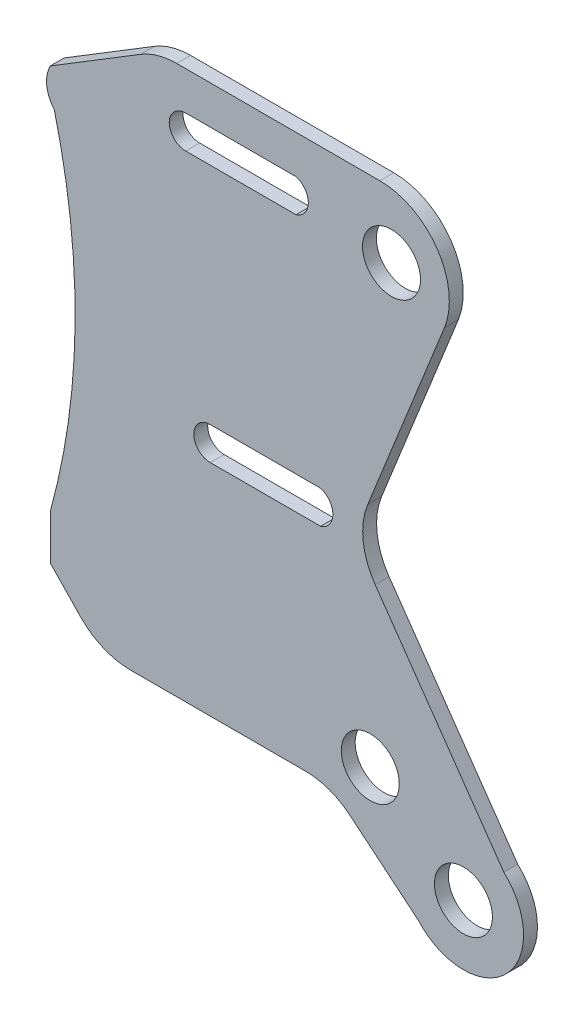
SolidWorks part; units mm, degrees
ref_plane "Plano frontal" through (0, 0, 0) normal (0, 0, 1) x (1, 0, 0)
ref_plane "Plano superior" through (0, 0, 0) normal (0, 1, 0) x (1, 0, 0)
ref_plane "Plano direito" through (0, 0, 0) normal (1, 0, 0) x (0, 0, -1)
sketch "Esboço1" plane through (0, 0, 0) normal (0, 0, 1) x (1, 0, 0)
  line L0 (341.3333, 723.5) -> (1706.6667, 723.5) construction
  line L1 (7335.8452, 5491.2568) -> (7400.7844, 5530.9769)
  line L2 (7426.8737, 5538.323) -> (7573.0613, 5538.323)
  line L3 (7619.4721, 5469.721) -> (7564.3004, 5332.0717)
  line L4 (7569.6809, 5284.895) -> (7662.3361, 5151.8513)
  line L5 (7335.8452, 5213.7223) -> (7335.8452, 5181.426)
  line L6 (7335.8452, 5181.426) -> (7357.5194, 5158.8955)
  line L7 (7393.5529, 5143.5595) -> (7519.5195, 5143.5595)
  line L8 (7551.4173, 5132.0632) -> (7600.7996, 5091.1533)
  line L9 (7512.7348, 5486.9744) -> (7433.3206, 5486.9744)
  line L10 (7530.4236, 5301.6208) -> (7451.0095, 5301.6208)
  line L11 (7433.3206, 5510.6721) -> (7512.7348, 5510.6721)
  line L12 (7451.0095, 5325.3184) -> (7530.4236, 5325.3184)
  arc A0 (7335.8452, 5491.2568) -> (7338.7563, 5465.3945) centre (7356.276, 5480.4615) ccw
  arc A1 (7338.7563, 5465.3945) -> (7335.8452, 5213.7223) centre (6862.8993, 5345.0458) cw
  arc A2 (7600.7996, 5091.1533) -> (7662.3361, 5151.8513) centre (7633.2164, 5119.8309) ccw
  arc A3 (7573.0613, 5538.323) -> (7619.4721, 5469.721) centre (7573.0613, 5488.323) cw
  arc A4 (7400.7844, 5530.9769) -> (7426.8737, 5538.323) centre (7426.8737, 5488.323) cw
  arc A5 (7357.5194, 5158.8955) -> (7393.5529, 5143.5595) centre (7393.5529, 5193.5595) ccw
  arc A6 (7519.5195, 5143.5595) -> (7551.4173, 5132.0632) centre (7519.5195, 5093.5595) cw
  arc A7 (7564.3004, 5332.0717) -> (7569.6809, 5284.895) centre (7610.7112, 5313.4696) ccw
  circle A8 centre (7566.1748, 5169.2953) radius 20.8633
  circle A9 centre (7633.2164, 5119.8309) radius 20.8633
  circle A10 centre (7581.432, 5491.2568) radius 20.8633
  arc A11 (7512.7348, 5510.6721) -> (7512.7348, 5486.9744) centre (7509.1866, 5498.8232) cw
  arc A12 (7433.3206, 5510.6721) -> (7433.3206, 5486.9744) centre (7433.3206, 5498.8232) ccw
  arc A13 (7530.4236, 5325.3184) -> (7530.4236, 5301.6208) centre (7526.8755, 5313.4696) cw
  arc A14 (7451.0095, 5325.3184) -> (7451.0095, 5301.6208) centre (7451.0095, 5313.4696) ccw
  point P20 (7412.7948, 5538.323)
  point P23 (7372.2726, 5143.5595)
  point P26 (7537.5401, 5143.5595)
  point P29 (7554.2641, 5307.0319)
  dimension "D5" = 32.2963
  dimension "D2" = 50
  dimension "D3" = 50
  dimension "D1" = 90.2024
  dimension "D4" = 189.1046
  dimension "D6" = 52.5436
  dimension "D7" = 165.2675
  dimension "D8" = 82.1473
  dimension "D10" = 23.6976
extrude "Ressalto-extrusão1" add sketch "Esboço1" along normal blind 10
